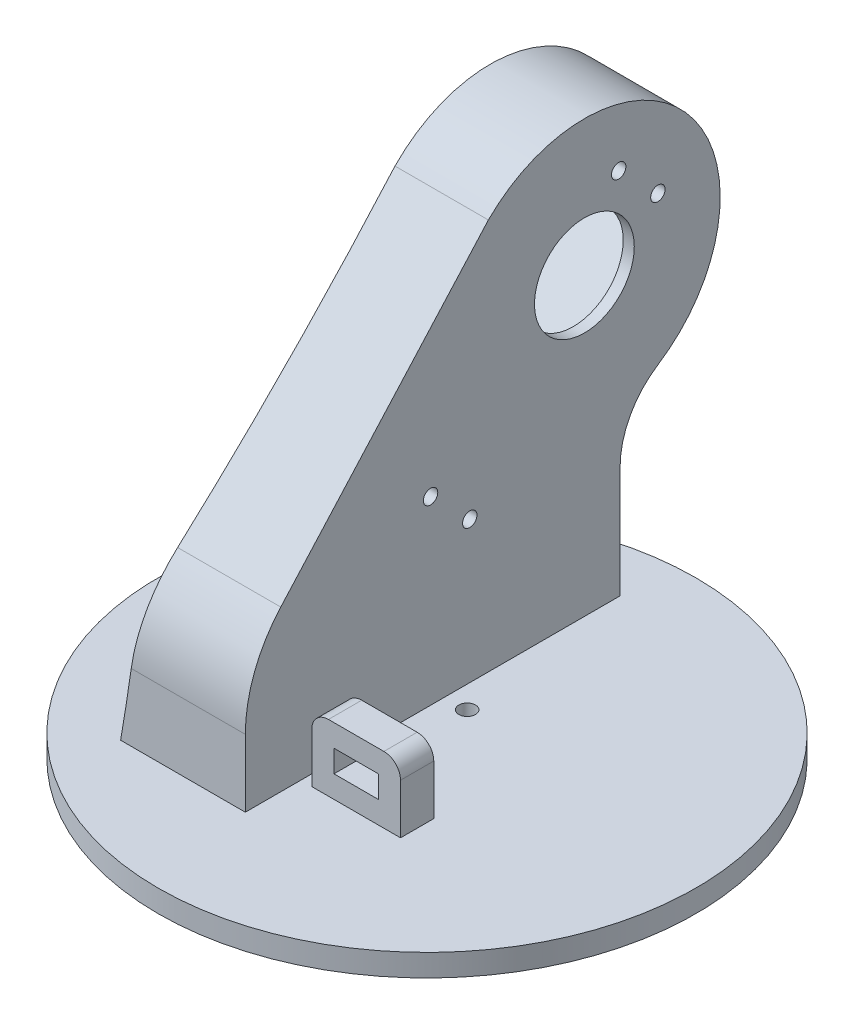
SolidWorks part; units mm, degrees
ref_plane "Front Plane" through (0, 0, 0) normal (0, 0, 1) x (1, 0, 0)
ref_plane "Top Plane" through (0, 0, 0) normal (0, 1, 0) x (1, 0, 0)
ref_plane "Right Plane" through (0, 0, 0) normal (1, 0, 0) x (0, 0, -1)
sketch "Sketch2" plane through (0, 0, 0) normal (0, 1, 0) x (1, 0, 0)
  circle A0 centre (0, 0) radius 48.5
  dimension "D1" = 97
extrude "Boss-Extrude1" add sketch "Sketch2" along normal blind 4
sketch "Sketch4" plane through (0, 0, 0) normal (0, -1, 0) x (1, 0, 0)
  circle A0 centre (0, 7.25) radius 1.5
  circle A1 centre (0, -7.25) radius 1.5
  dimension "D1" = 3
  dimension "D2" = 3
  dimension "D3" = 14.5
  dimension "D4" = 7.25
extrude "Cut-Extrude2" cut sketch "Sketch4" against normal through all
sketch "Sketch5" plane through (0, 0, 0) normal (0, -1, 0) x (1, 0, 0)
  circle A0 centre (0, 0) radius 3.75
  dimension "D1" = 7.5
extrude "Cut-Extrude3" cut sketch "Sketch5" against normal blind 1.5
ref_plane "Plane1" through (-4, 0, 0) normal (1, 0, 0) x (0, 0, -1)
sketch "Sketch7" plane through (-4, 0, 0) normal (1, 0, 0) x (0, 0, -1)
  line L0 (35.8382, 24.1161) -> (35.8382, 4)
  line L5 (48.5, 4) -> (-48.5, 4) construction
  line L6 (-21.4541, 33.8453) -> (17.1928, 72.4921)
  line L7 (-43.5609, 4) -> (35.8382, 4)
  line L11 (-28.7764, 4) -> (-28.7764, 16.1676)
  arc A4 (44.0669, 39.233) -> (17.1928, 72.4921) centre (32.3956, 57.2893) ccw
  arc A5 (44.0669, 39.233) -> (35.8382, 24.1161) centre (53.8382, 24.1161) ccw
  arc A6 (-21.4541, 33.8453) -> (-28.7764, 16.1676) centre (-3.7764, 16.1676) ccw
  point P5 (0, 0)
  point P6 (-28.7764, 16.1676)
  point P7 (35.8382, 4)
  dimension "D1" = 25
  dimension "D4" = 43
  dimension "D3" = 18
  dimension "D5" = 45
extrude "Boss-Extrude2" add sketch "Sketch7" against normal blind 14
ref_plane "Plane2" through (-6, 0, 0) normal (1, 0, 0) x (0, 0, -1)
sketch "Sketch8" plane through (-6, 0, 0) normal (1, 0, 0) x (0, 0, -1)
  line L0 (-21.4541, 33.8453) -> (17.1928, 72.4921) construction
  line L1 (3.2275, 42.9704) -> (32.2188, 71.9618)
  line L2 (3.2275, 42.9704) -> (18.0767, 28.1212)
  line L3 (18.0767, 28.1212) -> (47.0681, 57.1126)
  line L4 (32.2188, 71.9618) -> (47.0681, 57.1126)
  line L5 (3.2275, 42.9704) -> (47.0681, 57.1126) construction
  line L6 (18.0767, 28.1212) -> (32.2188, 71.9618) construction
  point P0 (25.1478, 50.0415)
  point P11 (32.3956, 57.2893)
  dimension "D1" = 41
  dimension "D2" = 21
  dimension "D3" = 90
  dimension "D4" = 20.5
  dimension "D5" = 90
  dimension "D6" = 10.25
  dimension "D7" = 10.5
extrude "Cut-Extrude5" cut sketch "Sketch8" against normal up to next
sketch "Sketch9" plane through (-18, 0, 0) normal (-1, 0, 0) x (0, 0, 1)
  line L0 (-32.2188, 71.9618) -> (-47.0681, 57.1126) construction
  line L3 (-39.6435, 64.5372) -> (-23.2681, 48.1619) construction
  circle A0 centre (-38.5828, 70.5476) radius 1.3
  circle A1 centre (-45.6539, 63.4765) radius 1.3
  circle A2 centre (-11.7127, 29.5354) radius 1.3
  circle A3 centre (-4.6417, 36.6065) radius 1.3
  dimension "D1" = 2.6
  dimension "D5" = 5
  dimension "D6" = 90
  dimension "D2" = 3.5
  dimension "D3" = 2
  dimension "D4" = 2
extrude "Cut-Extrude6" cut sketch "Sketch9" against normal through all
sketch "Sketch11" plane through (-4, 0, 0) normal (1, 0, 0) x (0, 0, -1)
  circle A0 centre (32.3956, 57.2893) radius 9
  dimension "D1" = 18
extrude "Cut-Extrude9" cut sketch "Sketch11" against normal up to next
sketch "Sketch17" plane through (-18, 0, 0) normal (-1, 0, 0) x (0, 0, 1)
  line L0 (23.5754, 35.9666) -> (-15.0715, 74.6135)
  line L1 (-38.8382, 24.1161) -> (-38.8382, 1)
  line L2 (-38.8382, 1) -> (31.7764, 1)
  line L3 (31.7764, 1) -> (31.7764, 16.1676)
  line L4 (21.4541, 33.8453) -> (-17.1928, 72.4921)
  line L5 (-35.8382, 24.1161) -> (-35.8382, 4)
  line L6 (-35.8382, 4) -> (28.7764, 4)
  line L7 (28.7764, 4) -> (28.7764, 16.1676)
  line L9 (-35.8382, 24.1161) -> (-35.8382, 4)
  line L10 (-35.8382, 4) -> (28.7764, 4)
  line L11 (28.7764, 4) -> (28.7764, 16.1676)
  line L12 (-38.8382, 4) -> (31.7764, 4)
  line L13 (48.5, 4) -> (-48.5, 4) construction
  line L14 (-15.0715, 74.6135) -> (22.3852, 32.8623)
  line L15 (-17.1928, 72.4921) -> (20.1533, 30.8577)
  line L16 (25.7764, 16.1676) -> (25.7764, 4)
  line L18 (21.4541, 33.8453) -> (-17.1928, 72.4921) construction
  arc A0 (-15.0715, 74.6135) -> (-45.6955, 36.7135) centre (-32.3956, 57.2893) ccw
  arc A1 (-38.8382, 24.1161) -> (-45.6955, 36.7135) centre (-53.8382, 24.1161) ccw
  arc A2 (31.7764, 16.1676) -> (23.5754, 35.9666) centre (3.7764, 16.1676) ccw
  arc A3 (-17.1928, 72.4921) -> (-44.0669, 39.233) centre (-32.3956, 57.2893) ccw
  arc A4 (-35.8382, 24.1161) -> (-44.0669, 39.233) centre (-53.8382, 24.1161) ccw
  arc A5 (28.7764, 16.1676) -> (21.4541, 33.8453) centre (3.7764, 16.1676) ccw
  arc A6 (-17.1928, 72.4921) -> (-44.0669, 39.233) centre (-32.3956, 57.2893) ccw
  arc A7 (-35.8382, 24.1161) -> (-44.0669, 39.233) centre (-53.8382, 24.1161) ccw
  arc A8 (28.7764, 16.1676) -> (21.4541, 33.8453) centre (3.7764, 16.1676) ccw
  arc A9 (25.7764, 16.1676) -> (19.3327, 31.724) centre (3.7764, 16.1676) ccw
  line M16 (21.4541, 33.8453) -> (-17.1928, 72.4921)
  arc M17 (-17.1928, 72.4921) -> (-44.0669, 39.233) centre (-32.3956, 57.2893) ccw
  arc M18 (-44.0669, 39.233) -> (-35.8382, 24.1161) centre (-53.8382, 24.1161) cw
  line M19 (-35.8382, 24.1161) -> (-35.8382, 4)
  line M21 (28.7764, 4) -> (28.7764, 16.1676)
  arc M22 (28.7764, 16.1676) -> (21.4541, 33.8453) centre (3.7764, 16.1676) ccw
  dimension "D1" = 0
  dimension "D2" = 3
  dimension "D3" = 3
extrude "Boss-Extrude7" add sketch "Sketch17" along normal blind 9 and the other way up to surface (14 mm away) contours A9 L16 L12 L15 M21 M22 M16 | A1 L1 L12 L14 A0 M19 M18 M17 M16 M22 other way up to face at (-4, 57.2893, -41.3956)
sketch "Sketch25" plane through (-18, 0, 0) normal (-1, 0, 0) x (0, 0, 1)
  line L0 (-35.8382, 24.1161) -> (-35.8382, 4)
  line L1 (48.5, 4) -> (-48.5, 4) construction
  line L2 (-35.8382, 24.1161) -> (-35.8382, 4) construction
  line L3 (-17.1928, 72.4921) -> (20.1533, 30.8577) construction
  line L4 (25.7764, 4) -> (-35.8382, 4) construction
  line L5 (25.7764, 16.1676) -> (25.7764, 4) construction
  line L6 (25.7764, 4) -> (-35.8382, 4)
  line L7 (25.7764, 16.1676) -> (25.7764, 4)
  line L8 (-17.1928, 72.4921) -> (20.1533, 30.8577)
  arc A0 (-35.8382, 24.1161) -> (-44.0669, 39.233) centre (-53.8382, 24.1161) ccw construction
  arc A1 (-17.1928, 72.4921) -> (-44.0669, 39.233) centre (-32.3956, 57.2893) ccw construction
  arc A2 (-35.8382, 24.1161) -> (-44.0669, 39.233) centre (-53.8382, 24.1161) ccw
  arc A3 (25.7764, 16.1676) -> (20.1533, 30.8577) centre (3.7764, 16.1676) ccw construction
  arc A4 (25.7764, 16.1676) -> (20.1533, 30.8577) centre (3.7764, 16.1676) ccw
  spline S0 degree 3 poles (-44.0669, 39.233) (-36.2174, 34.1592) (-9.6691, 17.1056) (-27.8382, 4) knots 0 0 0 0 1 1 1 1
  spline S1 degree 2 poles (10.6497, 41.4525) (25.9819, 24.3598) (19.7764, 4) knots 0 0 0 1 1 1
  dimension "D2" = 8
  dimension "D1" = 6
extrude "Boss-Extrude10" add sketch "Sketch25" along normal up to surface (9 mm away) contours S0 L6 L0 A2 | A4 S1 A2 S0 L8 up to face at (-27, 29.8809, -10.9189)
sketch "Sketch26" plane through (0, 0, 0) normal (0, 0, 1) x (1, 0, 0)
  line L0 (-4, 81.7893) -> (-27, 81.7893) construction
  line L1 (-27, 4) -> (-4, 4) construction
  line L2 (-27, 4) -> (-27, 16.1676) construction
  line L3 (-26, 81.7893) -> (-27, 81.7893)
  line L4 (-27, 81.7893) -> (-27, 4)
  line L5 (-27, 4) -> (-23, 4)
  spline S0 degree 2 poles (-26, 81.7893) (-25.5741, 42.8529) (-23, 4) knots 0 0 0 1 1 1
  dimension "D1" = 1
  dimension "D2" = 4
  dimension "D3" = 2
extrude "Cut-Extrude15" [suppressed] cut sketch "Sketch26" against normal through all both and the other way through all contours L4 L5 S0 L3
sketch "Sketch27" plane through (0, 4, 0) normal (0, 1, 0) x (1, 0, 0)
  line L1 (-2, -12.7764) -> (14, -12.7764)
  line L2 (-2, -12.7764) -> (-2, -18.7764)
  line L3 (-2, -18.7764) -> (14, -18.7764)
  line L4 (14, -12.7764) -> (14, -18.7764)
  line L5 (-27, -28.7764) -> (-4, -28.7764) construction
  line L6 (-4, -28.7764) -> (-4, 38.8382) construction
  dimension "D1" = 10
  dimension "D2" = 6
  dimension "D3" = 16
  dimension "D4" = 2
extrude "Boss-Extrude11" add sketch "Sketch27" along normal blind 12
fillet "Fillet6" radius 3 2 edges at (14, 16, 15.7764) (-2, 16, 15.7764)
sketch "Sketch28" plane through (0, 0, 18.7764) normal (0, 0, 1) x (1, 0, 0)
  line L8 (10, 12) -> (2, 12)
  line L9 (2, 12) -> (2, 8)
  line L10 (2, 8) -> (10, 8)
  line L11 (10, 8) -> (10, 12)
  line L12 (10, 12) -> (2, 12)
  line L13 (2, 12) -> (2, 8)
  line L14 (2, 8) -> (10, 8)
  line L15 (10, 8) -> (10, 12)
  dimension "D1" = 4
extrude "Cut-Extrude16" cut sketch "Sketch28" against normal up to next
sketch "Sketch29" plane through (0, 0, 0) normal (0, 0, 1) x (1, 0, 0)
  line L0 (-4, 81.7893) -> (-27, 81.7893) construction
  line L1 (-27, 4) -> (-4, 4) construction
  line L2 (-21, 81.7893) -> (-27, 81.7893)
  line L3 (-27, 81.7893) -> (-27, 4)
  line L4 (-27, 4) -> (-26.5, 4)
  line L5 (48.5, 4) -> (-48.5, 4) construction
  spline S0 degree 2 poles (-21, 81.7893) (-19.8157, 42.5456) (-26.5, 4) knots 0 0 0 1 1 1
  dimension "D1" = 6
  dimension "D2" = 4
  dimension "D3" = 0.5
  dimension "D4" = 25
extrude "Cut-Extrude17" cut sketch "Sketch29" against normal through all both and the other way through all
